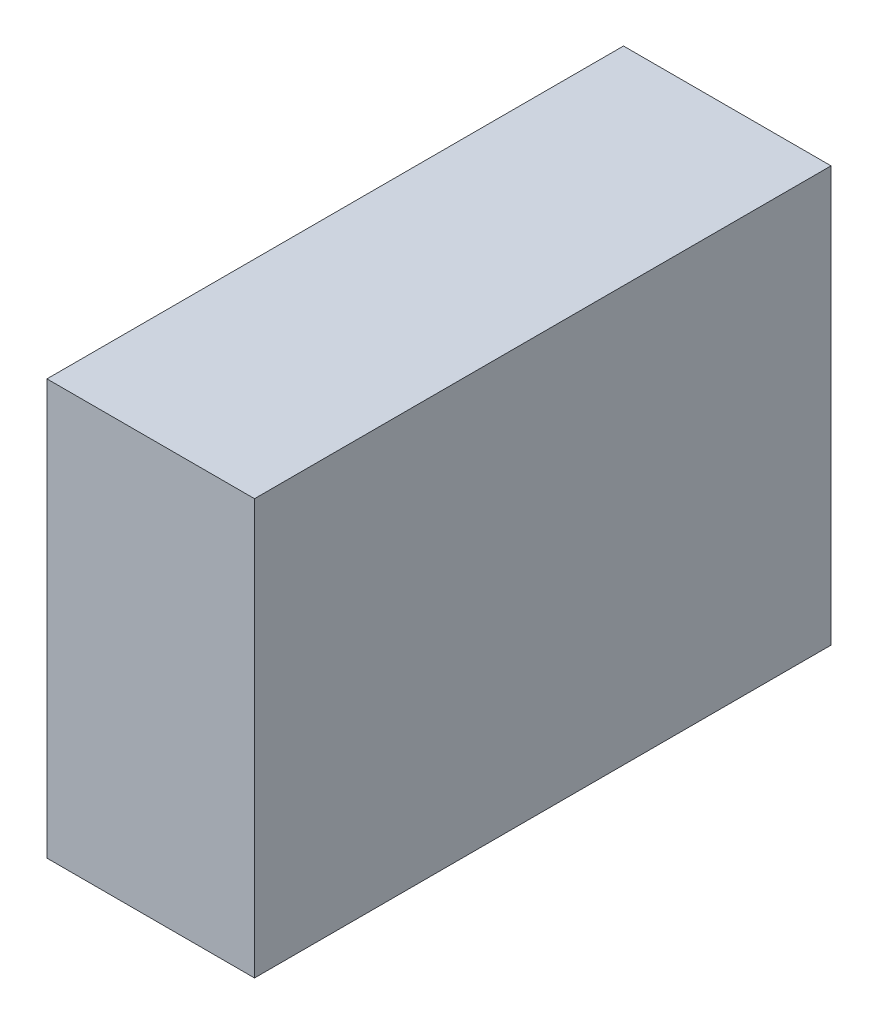
SolidWorks part; units mm, degrees
ref_plane "Piano frontale" through (0, 0, 0) normal (0, 0, 1) x (1, 0, 0)
ref_plane "Piano superiore" through (0, 0, 0) normal (0, 1, 0) x (1, 0, 0)
ref_plane "Piano destro" through (0, 0, 0) normal (1, 0, 0) x (0, 0, -1)
sketch "Schizzo1" plane through (0, 0, 0) normal (0, 0, 1) x (1, 0, 0)
  line L0 (9, 36) -> (9, 0) construction
  line L1 (0, 0) -> (18, 0)
  line L2 (0, 0) -> (0, 36)
  line L3 (0, 36) -> (18, 36)
  line L4 (18, 0) -> (18, 36)
  dimension "D1" = 36
  dimension "D2" = 18
extrude "Estrusione-Estrusione1" add sketch "Schizzo1" along normal blind 50
